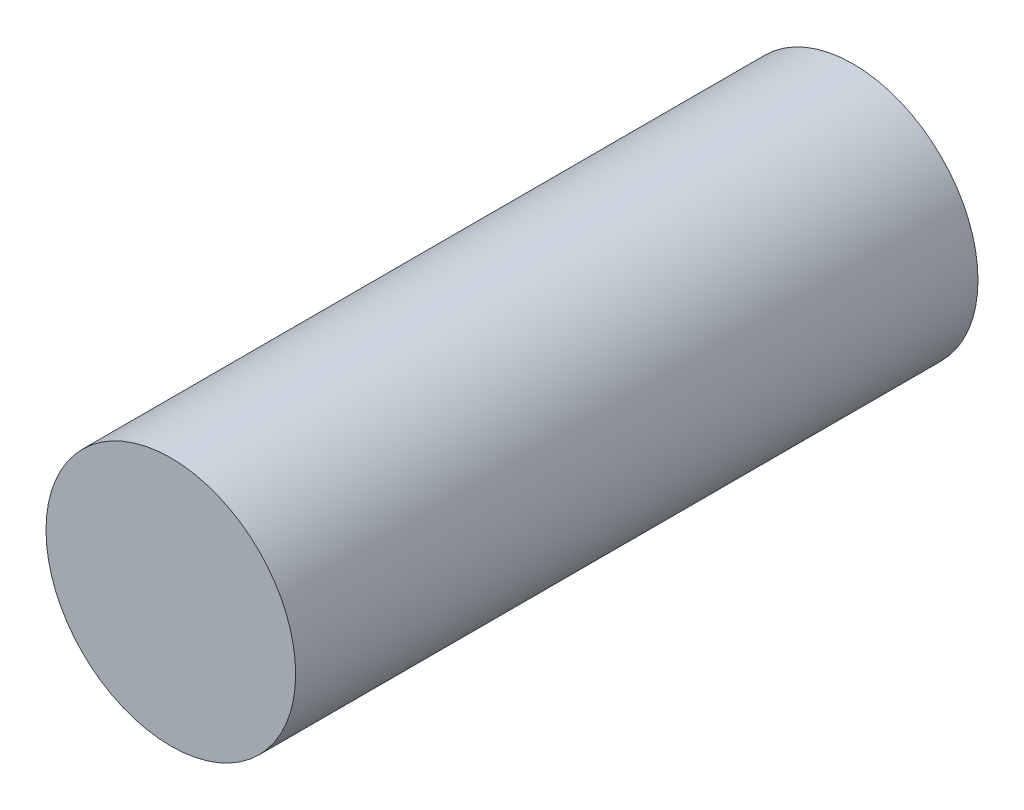
SolidWorks part; units mm, degrees
ref_plane "Ebene vorne" through (0, 0, 0) normal (0, 0, 1) x (1, 0, 0)
ref_plane "Ebene oben" through (0, 0, 0) normal (0, 1, 0) x (1, 0, 0)
ref_plane "Ebene rechts" through (0, 0, 0) normal (1, 0, 0) x (0, 0, -1)
sketch "Sketch1" plane through (0, 0, 0) normal (0, 0, 1) x (1, 0, 0)
  circle A0 centre (0, 0) radius 3
  dimension "D1" = 6
extrude "Boss-Extrude1" add sketch "Sketch1" along normal blind 16.4
